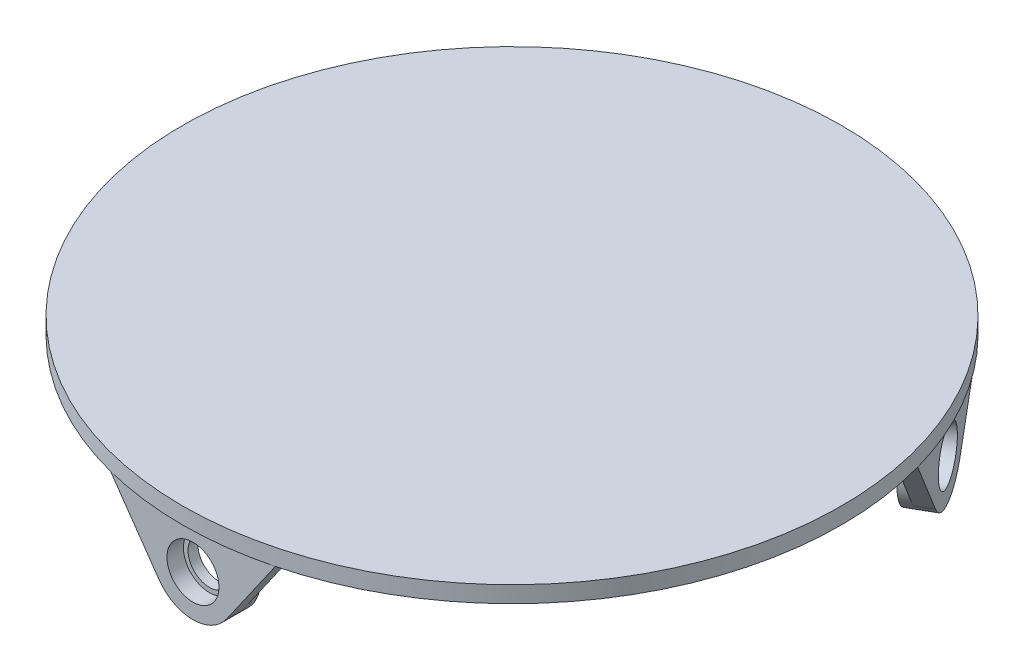
SolidWorks part; units mm, degrees
ref_plane "Front Plane" through (0, 0, 0) normal (0, 0, 1) x (1, 0, 0)
ref_plane "Top Plane" through (0, 0, 0) normal (0, 1, 0) x (1, 0, 0)
ref_plane "Right Plane" through (0, 0, 0) normal (1, 0, 0) x (0, 0, -1)
sketch "Sketch1" plane through (0, 0, 0) normal (0, 1, 0) x (1, 0, 0)
  circle A4 centre (0, 0) radius 100
  dimension "D1" = 200
extrude "Boss-Extrude2" add sketch "Sketch1" along normal blind 5
sketch "Sketch4" plane through (0, 0, 0) normal (0, -1, 0) x (1, 0, 0)
  line L0 (-25, 96.8246) -> (25, 96.8246)
  line L4 (25, 96.8246) -> (25, 91.8246)
  line L5 (25, 91.8246) -> (-25, 91.8246)
  line L6 (-25, 91.8246) -> (-25, 96.8246)
  circle A3 centre (0, 0) radius 100 construction
  dimension "D1" = 5
  dimension "D2" = 5
  dimension "D4" = 50
extrude "Boss-Extrude4" add sketch "Sketch4" along normal blind 30
sketch "Sketch6" plane through (0, 0, 91.8246) normal (0, 0, -1) x (-1, 0, 0)
  line L1 (25, 0) -> (10.2536, -21.1493)
  line L2 (-25, 0) -> (-10.2536, -21.1493)
  line L3 (-25, 0) -> (-25, -30.8132)
  line L4 (-25, -30.8132) -> (25, -30.8132)
  line L5 (25, -30.8132) -> (25, 0)
  line L7 (-100, 0) -> (100, 0) construction
  line L8 (0, 0) -> (0, -14) construction
  arc A0 (-10.2536, -21.1493) -> (10.2536, -21.1493) centre (0, -14) ccw
  circle A1 centre (0, -14) radius 7.89
  dimension "D1" = 25
  dimension "D2" = 15.78
  dimension "D3" = 14
extrude "Cut-Extrude1" cut sketch "Sketch6" against normal up to next (5 mm away)
pattern_circular "CirPattern2" count 3 every 120 about axis through (0, 0, 0) along (0, 1, 0) of "Boss-Extrude4", "Cut-Extrude1"
sketch "Sketch8" plane through (0, 0, 91.8246) normal (0, 0, -1) x (-1, 0, 0)
  circle A0 centre (0, -14) radius 12.5
  circle A1 centre (0, -14) radius 6.5
  dimension "D1" = 13
  dimension "D2" = 25
extrude "Boss-Extrude5" add sketch "Sketch8" along normal blind 3
pattern_circular "CirPattern3" count 3 every 120 about axis through (0, 0, 0) along (0, 1, 0) of "Boss-Extrude5"
